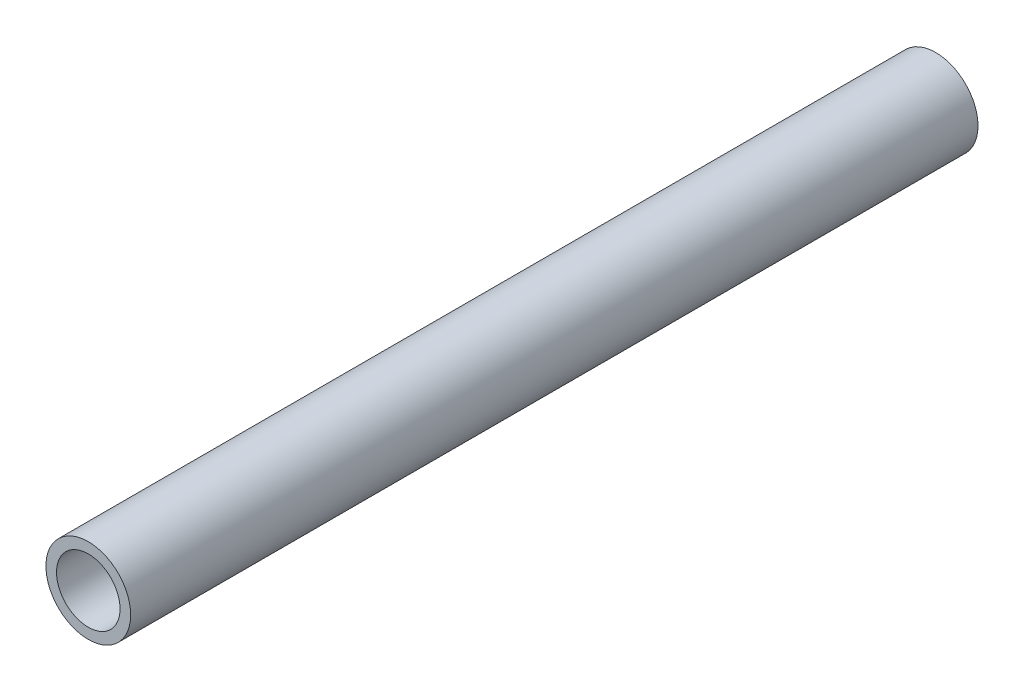
SolidWorks part; units mm, degrees
ref_plane "Alzado" through (0, 0, 0) normal (0, 0, 1) x (1, 0, 0)
ref_plane "Planta" through (0, 0, 0) normal (0, 1, 0) x (1, 0, 0)
ref_plane "Vista lateral" through (0, 0, 0) normal (1, 0, 0) x (0, 0, -1)
sketch "Croquis1" plane through (0, 0, 0) normal (0, 0, 1) x (1, 0, 0)
  circle A0 centre (0, 0) radius 4
  circle A1 centre (0, 0) radius 3
  dimension "D1" = 6
  dimension "D2" = 8
extrude "Saliente-Extruir1" add sketch "Croquis1" along normal blind 80
